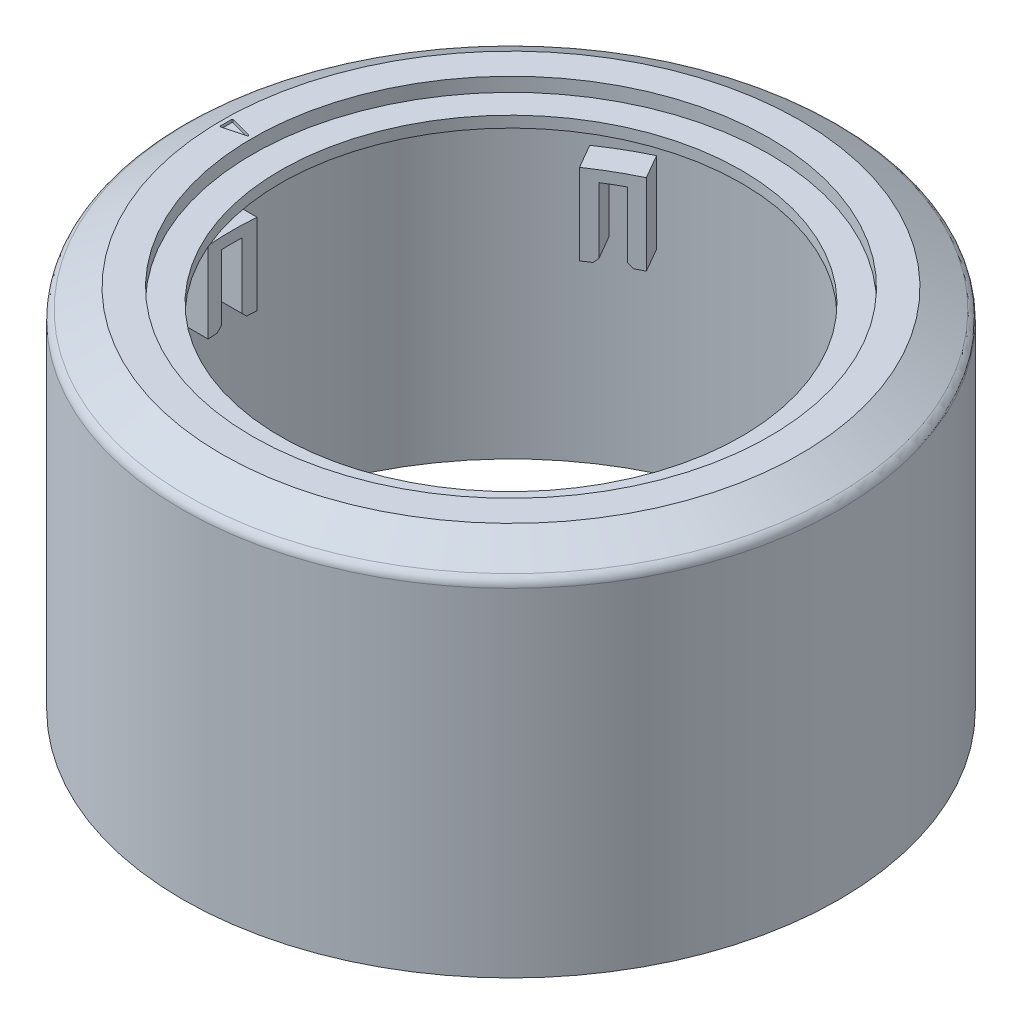
SolidWorks part; units mm, degrees
ref_plane "前视基准面" through (0, 0, 0) normal (0, 0, 1) x (1, 0, 0)
ref_plane "上视基准面" through (0, 0, 0) normal (0, 1, 0) x (1, 0, 0)
ref_plane "右视基准面" through (0, 0, 0) normal (1, 0, 0) x (0, 0, -1)
sketch "草图1" plane through (0, 0, 0) normal (0, 0, 1) x (1, 0, 0)
  line L0 (0, 0) -> (0, 74.5632) construction
  line L1 (-22, 0) -> (-23.5, 0)
  line L2 (-23.5, 0) -> (-23.5, 24.1503)
  line L3 (-23.1249, 24.8) -> (-20.7, 26.2)
  line L4 (-20.7, 26.2) -> (-18.5, 26.2)
  line L5 (-18.5, 26.2) -> (-18.5, 25.2)
  line L6 (-18.5, 25.2) -> (-16.5, 25.2)
  line L7 (-16.5, 25.2) -> (-16.5, 24.4)
  line L8 (-16.5, 24.4) -> (-22, 24.4)
  line L9 (-22, 24.4) -> (-22, 0)
  line L10 (0, 0) -> (-83.5811, 0) construction
  line L11 (-20.7, 26.2) -> (-21.7643, 26.2) construction
  arc A0 (-23.5, 24.1503) -> (-23.1249, 24.8) centre (-22.7497, 24.1503) cw
  dimension "D1" = 24.4
  dimension "D2" = 0.8
  dimension "D3" = 1
  dimension "D4" = 2
  dimension "D5" = 44
  dimension "D6" = 1.5
  dimension "D7" = 33
  dimension "D8" = 30
  dimension "D9" = 2.2
  dimension "D10" = 2.8
revolve "旋转1" add sketch "草图1" angle 360 about L0
ref_plane "基准面2" through (-23.5, 0, 0) normal (-1, 0, 0) x (0, 0, 1)
sketch "草图5" plane through (-23.5, 0, 0) normal (-1, 0, 0) x (0, 0, 1)
  line L0 (-16.5, 24.4) -> (16.5, 24.4) construction
  line L1 (-16.5, 24.4) -> (16.5, 24.4) construction
  line L2 (0, 0) -> (0, 24.2572) construction
  line L3 (-0.75, 13.9) -> (-0.75, 18.9)
  line L4 (-0.75, 18.9) -> (0.75, 18.9)
  line L5 (0.75, 18.9) -> (0.75, 13.9)
  line L6 (0.75, 13.9) -> (1.75, 13.9)
  line L7 (1.75, 13.9) -> (1.75, 19.7)
  line L8 (1.75, 19.7) -> (-1.75, 19.7)
  line L9 (-1.75, 19.7) -> (-1.75, 13.9)
  line L10 (-1.75, 13.9) -> (-0.75, 13.9)
  dimension "D1" = 1.5
  dimension "D2" = 5
  dimension "D3" = 0.8
  dimension "D4" = 5.5
  dimension "D5" = 1
extrude "凸台-拉伸5" add sketch "草图5" against normal blind 2 from surface starting at face at (0, 24.4, -22)
pattern_circular "阵列(圆周)2" count 6 over 360 about axis through (0, 0, 0) along (0, 1, 0) of "凸台-拉伸5"
sketch "草图6" plane through (0, 26.2, 0) normal (0, 1, 0) x (1, 0, 0)
  line L0 (0, 0) -> (-27.4096, 0) construction
  line L2 (-20.4, 0.4689) -> (-18.65, 0)
  line L3 (-20.4, 0.4689) -> (-20.4, -0.4689)
  line L4 (-20.4, -0.4689) -> (-18.65, 0)
  circle A0 centre (0, 0) radius 18.5 construction
  circle A1 centre (0, 0) radius 18.5 construction
  circle A2 centre (0, 0) radius 20.7 construction
  circle A3 centre (0, 0) radius 20.7 construction
  point P9 (-18.5, 0)
  point P13 (-20.7, 0)
  point P14 (-20.4, 0)
  dimension "D1" = 0.15
  dimension "D2" = 30
  dimension "D3" = 0.3
extrude "切除-拉伸1" cut sketch "草图6" against normal blind 0.2
fillet "圆角1" radius 0.05 3 edges at (-20.4, 26.1, 0.4689) (-18.65, 26.1, 0) (-20.4, 26.1, -0.4689)
chamfer "倒角1" distance 0.3 angle 45 12 edges at (-9.8441, 13.9, 18.5505) (-11.1431, 13.9, 17.8005) (11.1431, 13.9, 17.8005) (9.8441, 13.9, 18.5505) (20.9872, 13.9, 0.75) (20.9872, 13.9, -0.75) (11.1431, 13.9, -17.8005) (9.8441, 13.9, -18.5505) (-9.8441, 13.9, -18.5505) (-11.1431, 13.9, -17.8005) (-20.9872, 13.9, -0.75) (-20.9872, 13.9, 0.75)
